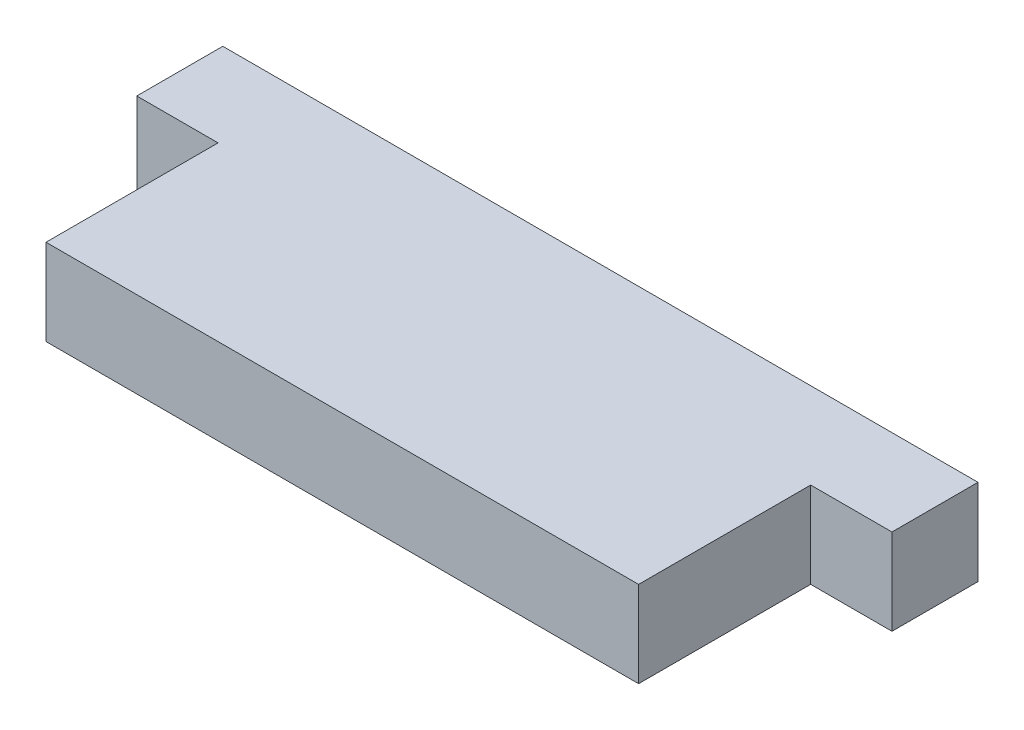
SolidWorks part; units mm, degrees
ref_plane "Front Plane" through (0, 0, 0) normal (0, 0, 1) x (1, 0, 0)
ref_plane "Top Plane" through (0, 0, 0) normal (0, 1, 0) x (1, 0, 0)
ref_plane "Right Plane" through (0, 0, 0) normal (1, 0, 0) x (0, 0, -1)
sketch "Sketch1" plane through (0, 0, 0) normal (0, 1, 0) x (1, 0, 0)
  line L0 (0, 0) -> (0, 12.7)
  line L1 (0, 0) -> (43.74, 0)
  line L3 (43.74, 0) -> (43.74, 12.7)
  line L4 (-6.0001, 19.05) -> (49.7401, 19.05)
  line L5 (-6.0001, 19.05) -> (-6.0001, 12.7)
  line L6 (49.7401, 19.05) -> (49.7401, 12.7)
  line L7 (-6.0001, 12.7) -> (0, 12.7)
  line L8 (43.74, 12.7) -> (49.7401, 12.7)
  dimension "D1" = 12.7
  dimension "D2" = 43.74
  dimension "D3" = 6.35
  dimension "D4" = 6.0001
  dimension "D5" = 6.0001
extrude "Boss-Extrude1" add sketch "Sketch1" along normal blind 6.35
equation "\"vigorwidth\"= 0.472441in"
equation "\"vigorflangewidth\"= 0.731102in"
equation "\"vigorflangelength\"= 0.131102in"
equation "\"vigorscrewsize\"= 0.066535in"
equation "\"vigorholeoffsetwid\"= 0.0646653in"
equation "\"vigorholeoffsetlen\"= 0.065551in"
equation "\"vigorflangedepth\"= 0.0901575in"
equation "\"vigordiscdepth\"= 0.0492126in"
equation "\"vigormotordepth\"= 1.12362in"
equation "\"vigortipdepth\"= 0.259055in"
equation "\"vigoraxlewidth\"= 0.173622in"
equation "\"vigorcutlen\"= 0.0480315in"
equation "\"vigoraxledepth\"= 0.159055in"
equation "\"rackoffset\"=.236224in"
equation "\"Slot\"=.25in"
equation "\"MotorMountLegLength\"=.25in"
equation "\"GearOffset\"=.264907in"
equation "\"D4@Sketch1\"=\"rackoffset\""
equation "\"D5@Sketch1\"=\"rackoffset\""
equation "\"MotorMountWidth\"=1.72204724"
equation "\"D2@Sketch1\"=\"MotorMountWidth\""
